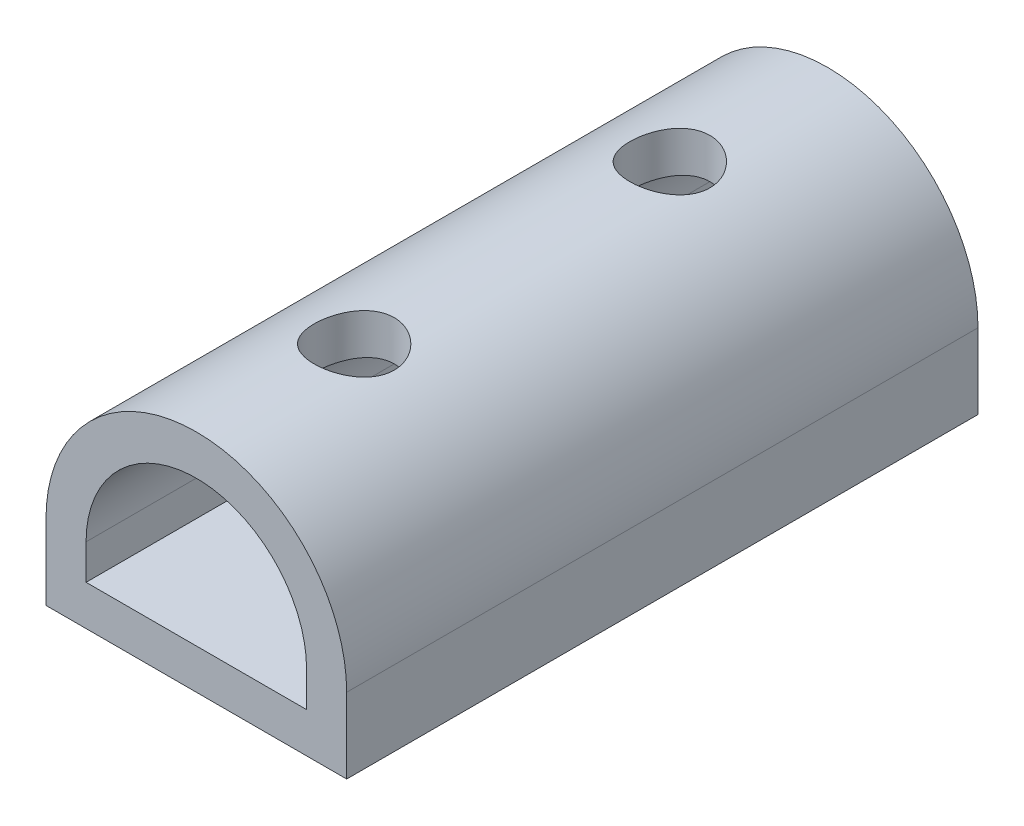
SolidWorks part; units mm, degrees
ref_plane "Front" through (0, 0, 0) normal (0, 0, 1) x (1, 0, 0)
ref_plane "Top" through (0, 0, 0) normal (0, 1, 0) x (1, 0, 0)
ref_plane "Right" through (0, 0, 0) normal (1, 0, 0) x (0, 0, -1)
sketch "Sketch1" plane through (0, 0, 0) normal (0, 0, 1) x (1, 0, 0)
  line L0 (-4.7625, -2.3812) -> (4.7625, -2.3812)
  line L1 (-4.7625, 0) -> (4.7625, 0) construction
  line L2 (-4.7625, 0) -> (-4.7625, -2.3812)
  line L3 (4.7625, 0) -> (4.7625, -2.3812)
  line L4 (-3.4925, -1.1112) -> (3.4925, -1.1112)
  line L5 (-3.4925, 0) -> (3.4925, 0) construction
  line L6 (-3.4925, 0) -> (-3.4925, -1.1112)
  line L7 (3.4925, 0) -> (3.4925, -1.1112)
  arc A0 (-4.7625, 0) -> (4.7625, 0) centre (0, 0) cw
  arc A1 (-3.4925, 0) -> (3.4925, 0) centre (0, 0) cw
  dimension "D1" = 9.525
  dimension "D2" = 2.3813
  dimension "D3" = 6.985
  dimension "D4" = 1.27
extrude "Boss-Extrude1" add sketch "Sketch1" along normal blind 20
sketch "Sketch2" plane through (0, -2.3812, 0) normal (0, -1, 0) x (-1, 0, 0)
  line L0 (-4.7625, -10) -> (4.7625, -10) construction
  line L1 (4.7625, -20) -> (4.7625, 0) construction
  line L2 (-4.7625, -20) -> (-4.7625, 0) construction
  line L3 (0, -15) -> (0, -5) construction
  circle A1 centre (0, -15) radius 1.27
  circle A2 centre (0, -5) radius 1.27
  point P1 (0, -10)
  dimension "D2" = 2.54
  dimension "D1" = 10
extrude "Cut-Extrude1" cut sketch "Sketch2" against normal up to surface (7.1437 mm away)
sketch "Sketch3" plane through (0, 0, 20) normal (0, 0, 1) x (1, 0, 0)
  line L0 (0, -1.1112) -> (0, -2.3812) construction
  line L1 (-3.4925, -1.1112) -> (3.4925, -1.1112) construction
  line L2 (-4.7625, -2.3812) -> (4.7625, -2.3812) construction
